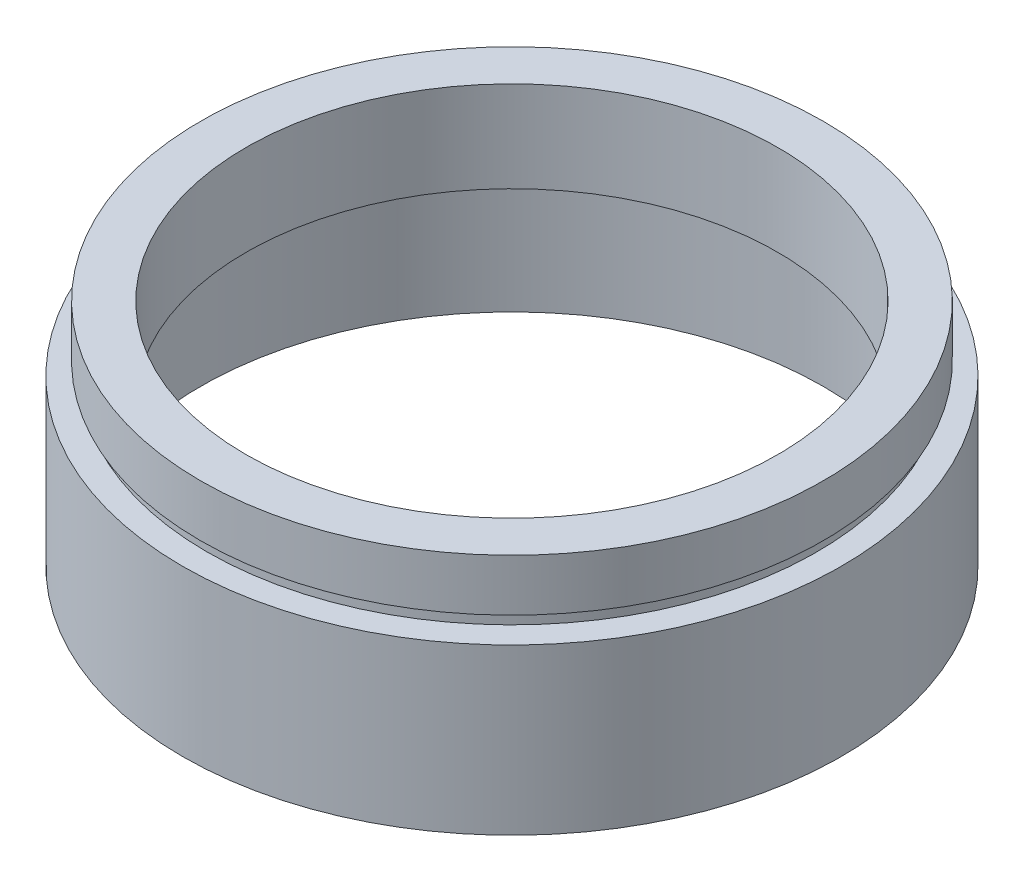
SolidWorks part; units mm, degrees
ref_plane "前视基准面" through (0, 0, 0) normal (0, 0, 1) x (1, 0, 0)
ref_plane "上视基准面" through (0, 0, 0) normal (0, 1, 0) x (1, 0, 0)
ref_plane "右视基准面" through (0, 0, 0) normal (1, 0, 0) x (0, 0, -1)
sketch "草图1" plane through (0, 0, 0) normal (0, 0, 1) x (1, 0, 0)
  line L0 (0, 161.3762) -> (0, 0) construction
  line L1 (141.7365, 0) -> (-131.7984, 0) construction
  line L2 (20.5, 17.7) -> (24, 17.7)
  line L3 (24, 17.7) -> (24, 13.7)
  line L4 (24, 13.7) -> (23.5, 13.7)
  line L5 (23.5, 13.7) -> (23.5, 12.7)
  line L6 (23.5, 12.7) -> (25.4, 12.7)
  line L7 (25.4, 12.7) -> (25.4, 0)
  line L8 (25.4, 0) -> (24, 0)
  line L9 (24, 0) -> (24, 9.7)
  line L10 (24, 9.7) -> (24.1, 9.7)
  line L11 (24.1, 9.7) -> (24.1, 10.7)
  line L12 (24.1, 10.7) -> (20.5, 10.7)
  line L13 (20.5, 10.7) -> (20.5, 17.7)
  dimension "D1" = 20.5
  dimension "D2" = 24
  dimension "D3" = 1
  dimension "D4" = 1
  dimension "D5" = 23.5
  dimension "D6" = 24.1
  dimension "D7" = 24
  dimension "D8" = 5
  dimension "D9" = 7
  dimension "D10" = 12.7
  dimension "D11" = 25.4
revolve "旋转1" add sketch "草图1" angle 360 about L0
cosmetic thread "装饰螺纹线1" parameters "D2"=52
cosmetic thread "装饰螺纹线2" parameters "D2"=48
cosmetic thread "装饰螺纹线3" parameters "D2"=45
